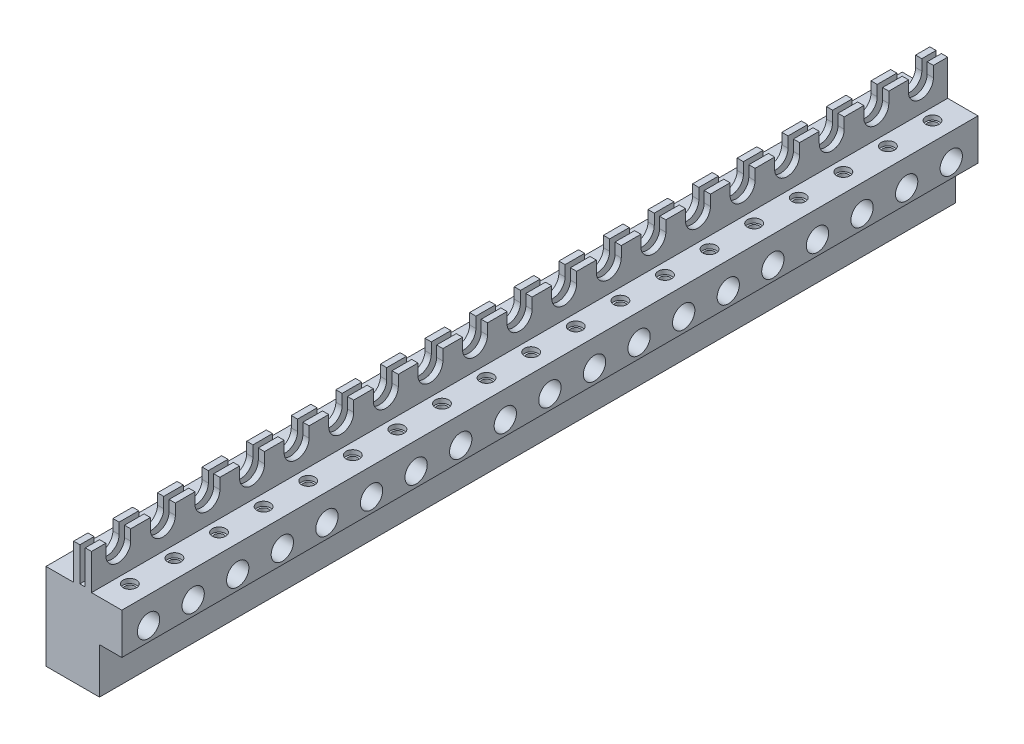
SolidWorks part; units mm, degrees
ref_plane "Front Plane" through (0, 0, 0) normal (0, 0, 1) x (1, 0, 0)
ref_plane "Top Plane" through (0, 0, 0) normal (0, 1, 0) x (1, 0, 0)
ref_plane "Right Plane" through (0, 0, 0) normal (1, 0, 0) x (0, 0, -1)
sketch "Sketch1" plane through (0, 0, 0) normal (0, 0, 1) x (1, 0, 0)
  line L1 (-4.25, -6.85) -> (4.25, -6.85)
  line L2 (-4.25, -6.85) -> (-4.25, 6.85)
  line L3 (-4.25, 6.85) -> (4.25, 6.85)
  line L4 (4.25, -6.85) -> (4.25, 6.85)
  line L5 (-4.25, -6.85) -> (4.25, 6.85) construction
  line L6 (-4.25, 6.85) -> (4.25, -6.85) construction
  point P0 (0, 0)
  dimension "D1" = 8.5
  dimension "D2" = 13.7
extrude "Boss-Extrude1" add sketch "Sketch1" against normal blind 96
sketch "Sketch2" plane through (0, 0, 0) normal (0, 0, 1) x (1, 0, 0)
  line L0 (4.25, 6.85) -> (-4.25, 6.85) construction
  line L1 (4.25, -6.85) -> (1.75, -6.85)
  line L2 (4.25, -6.85) -> (4.25, -1.75)
  line L3 (4.25, -1.75) -> (1.75, -1.75)
  line L4 (1.75, -6.85) -> (1.75, -1.75)
  line L5 (-4.25, 6.85) -> (-4.25, -6.85) construction
  dimension "D1" = 8.6
  dimension "D2" = 6
extrude "Cut-Extrude1" cut sketch "Sketch2" against normal through all
sketch "Sketch3" plane through (0, 0, 0) normal (0, 0, 1) x (1, 0, 0)
  line L0 (4.25, -1.75) -> (1.75, -1.75) construction
  line L1 (-4.25, 6.85) -> (-1.15, 6.85)
  line L2 (-4.25, 6.85) -> (-4.25, 2.85)
  line L3 (-4.25, 2.85) -> (-1.15, 2.85)
  line L4 (-1.15, 6.85) -> (-1.15, 2.85)
  line L5 (4.25, 6.85) -> (0.85, 6.85)
  line L6 (4.25, 6.85) -> (4.25, 2.85)
  line L7 (4.25, 2.85) -> (0.85, 2.85)
  line L8 (0.85, 6.85) -> (0.85, 2.85)
  line L9 (4.25, 6.85) -> (-4.25, 6.85) construction
  line L10 (-0.45, 6.85) -> (0.15, 6.85)
  line L11 (-0.45, 6.85) -> (-0.45, 3.05)
  line L12 (-0.45, 3.05) -> (0.15, 3.05)
  line L13 (0.15, 6.85) -> (0.15, 3.05)
  line L14 (-0.15, 3.05) -> (-0.15, 6.85) construction
  dimension "D1" = 4.6
  dimension "D2" = 4.1
  dimension "D3" = 2
  dimension "D4" = 0.6
  dimension "D5" = 1
  dimension "D6" = 3.8
extrude "Cut-Extrude2" cut sketch "Sketch3" against normal through all
sketch "Sketch4" plane through (0.85, 0, 0) normal (1, 0, 0) x (0, 0, -1)
  line L0 (1.6, 6.85) -> (1.6, 5.65)
  line L1 (96, 6.85) -> (0, 6.85) construction
  line L2 (4.4, 5.65) -> (4.4, 6.85)
  line L3 (4.4, 6.85) -> (1.6, 6.85)
  line L4 (0, 6.85) -> (0, 2.85) construction
  arc A0 (1.6, 5.65) -> (4.4, 5.65) centre (3, 5.65) ccw
  dimension "D1" = 2.6
  dimension "D2" = 1.6
  dimension "D3" = 2.8
extrude "Cut-Extrude3" cut sketch "Sketch4" against normal through all
pattern_linear "LPattern1" count 19 spacing 5 along (0, 0, -1) of "Cut-Extrude3"
sketch "Sketch5" plane through (4.25, 0, 0) normal (1, 0, 0) x (0, 0, -1)
  line L0 (96, 2.85) -> (0, 2.85) construction
  line L1 (3, 5.65) -> (3, -2.2393) construction
  circle A0 centre (3, -0.15) radius 1.25
  dimension "D1" = 3
  dimension "D2" = 2.5
extrude "Cut-Extrude4" cut sketch "Sketch5" against normal through all
pattern_linear "LPattern2" count 19 spacing 5 along (0, 0, -1) of "Cut-Extrude4"
hole_wizard "Ø1.8 (1.8) Diameter Hole1" positions "Sketch9" profile "Sketch10" hole size "Ø1.8" standard "DIN"
sketch "Sketch9" plane through (0, 2.85, 0) normal (0, 1, 0) x (-1, 0, 0)
  line L0 (0.8, -1.6) -> (0.8, -4.4) construction
  line L1 (1.15, -1.6) -> (0.45, -1.6) construction
  line L2 (1.15, -4.4) -> (0.45, -4.4) construction
  line L3 (0.8, -3) -> (5.4547, -3) construction
  line L4 (0.45, -3) -> (-0.15, -3) construction
  line L5 (0.45, -1.6) -> (0.45, -4.4) construction
  line L6 (-0.15, -4.4) -> (-0.15, -1.6) construction
  line L7 (0.15, -3) -> (0.15, 0.2827) construction
  point P0 (2.85, -3)
  dimension "D1" = 2.7
sketch "Sketch10" plane through (-2.85, 2.85, -3) normal (1, 0, 0) x (0, 0, 1)
  line L0 (0, 0) -> (0, 8.4552)
  line L1 (0, 8.4552) -> (0.9, 7.7)
  line L2 (0.9, 7.7) -> (0.9, 0)
  line L5 (0.9, 0) -> (0, 0)
  line L10 (0, 8.4552) -> (-0.9, 7.7) construction
  line L11 (0, -6.35) -> (0, 107.95) construction
  dimension "Hole Dia." = 1.8
  dimension "Hole Depth" = 7.7
  dimension "Drill Angle" = 100
pattern_linear "LPattern3" count 19 spacing 5 along (0, 0, -1) of "Ø1.8 (1.8) Diameter Hole1"
hole_wizard "M1.4x0.3 Tapped Hole1" positions "Sketch12" profile "Sketch13" tap size "M1.4x0.3" standard "ANSI Metric"
sketch "Sketch12" plane through (0, 2.85, 0) normal (0, 1, 0) x (-1, 0, 0)
  line L0 (2.85, -3) -> (-5.8661, -3) construction
  circle A0 centre (2.85, -3) radius 0.9 construction
  point P0 (-2.15, -3)
  dimension "D1" = 5
sketch "Sketch13" plane through (2.15, 2.85, -3) normal (1, 0, 0) x (0, 0, 1)
  line L0 (0, 0) -> (0, 4.6)
  line L1 (0, 4.6) -> (0.55, 4.6)
  line L2 (0.55, 4.6) -> (0.55, 0)
  line L5 (0.55, 0) -> (0, 0)
  line L11 (0, -6.35) -> (0, 107.95) construction
  dimension "Thru Tap Drill Dia." = 1.1
  dimension "Thru Tap Drill Depth" = 4.6
cosmetic thread "Hole Thread1" parameters "D2"=1.4
sketch "Sketch14" plane through (0, 2.85, 0) normal (0, 1, 0) x (1, 0, 0)
  circle A0 centre (2.15, 3) radius 0.75
  dimension "D1" = 1.5
extrude "Cut-Extrude5" cut sketch "Sketch14" against normal blind 0.5
pattern_linear "LPattern4" count 19 spacing 5 along (0, 0, -1) of "M1.4x0.3 Tapped Hole1", "Cut-Extrude5"
